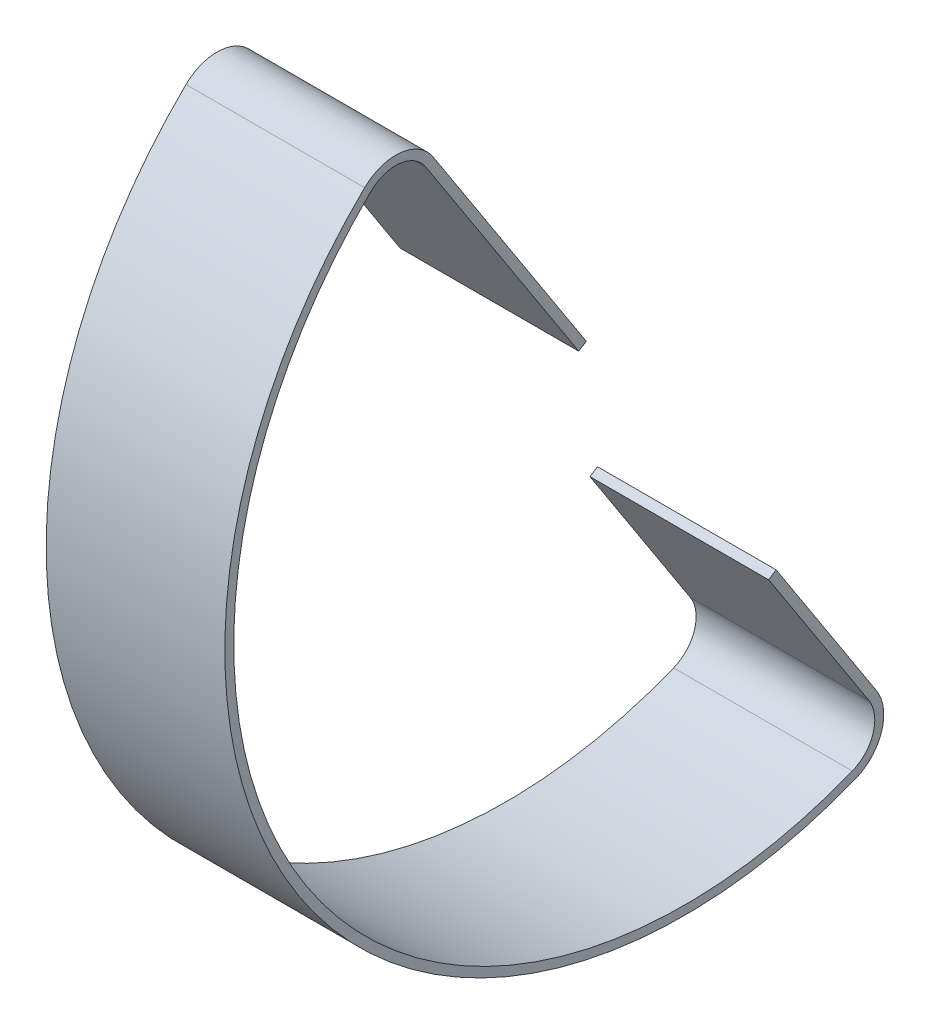
SolidWorks part; units mm, degrees
ref_plane "Front Plane" through (0, 0, 0) normal (0, 0, 1) x (1, 0, 0)
ref_plane "Top Plane" through (0, 0, 0) normal (0, 1, 0) x (1, 0, 0)
ref_plane "Right Plane" through (0, 0, 0) normal (1, 0, 0) x (0, 0, -1)
ref_plane "Plane1" through (1981.2, 0, 0) normal (1, 0, 0) x (0, 0, -1)
sketch "Sketch2" plane through (1981.2, 0, 0) normal (1, 0, 0) x (0, 0, -1)
  line L0 (221.3296, 149.9357) -> (209.5008, 142.2673) construction
  line L1 (221.3296, 149.9357) -> (209.184, 168.6708) construction
  line L2 (221.3296, 149.9357) -> (209.184, 168.6708) construction
  line L3 (273.5917, 69.3195) -> (285.7374, 50.5844) construction
  line L4 (273.5917, 69.3195) -> (285.7374, 50.5844) construction
  line L5 (220.4661, 151.2678) -> (176.9489, 218.3946)
  line L6 (274.4553, 67.9874) -> (303.0021, 23.953)
  line L7 (313.9939, 6.9977) -> (307.8258, 16.5121) construction
  line L8 (273.5917, 69.3195) -> (265.5737, 64.1215) construction
  line L9 (165.7975, 235.5961) -> (172.2848, 225.5893) construction
  line L10 (247.9458, 109.942) -> (151.6337, 47.5045) construction
  line L11 (151.6337, 47.5045) -> (142.0377, 41.2836) construction
  arc A0 (157.4526, 220.6047) -> (297.0616, 5.2526) centre (248.4911, 126.6943) ccw
  arc A1 (297.0616, 5.2526) -> (303.0021, 23.953) centre (292.3455, 17.0445) ccw
  arc A2 (176.9489, 218.3946) -> (157.4526, 220.6047) centre (166.2923, 211.4861) ccw
  spline S11 degree 3 poles (716.4378, 3936.626) (-41.01, 922.5586) (-45.8421, 102.7973) (199.57, -1.0271) (203.7349, -2.5525) (212.2057, -5.1923) (216.5116, -6.3067) (221.9842, -7.4366) (223.0832, -7.6494) (225.2905, -8.0483) (226.4002, -8.2347) (229.7298, -8.7513) (231.9491, -9.0392) (238.6058, -9.7364) (247.4783, -10.2233) (256.3445, -9.8408) (262.9919, -9.2245) (265.2072, -8.964) (268.5297, -8.4895) (269.6371, -8.3173) (271.8517, -7.9447) (272.9592, -7.7441) (278.4654, -6.6762) (282.7945, -5.61) (291.3052, -3.0674) (295.4869, -1.5909) (303.7034, 1.7715) (307.7383, 3.6574) (313.6773, 6.8016) (315.6425, 7.9051) (319.4945, 10.1955) (321.3853, 11.3842) (326.954, 15.0783) (334.1028, 20.3445) (340.7075, 26.2822) (345.4543, 30.9907) (347.0021, 32.6028) (349.271, 35.086) (350.0194, 35.9257) (351.4935, 37.6212) (352.2185, 38.4763) (355.7849, 42.7884) (358.4496, 46.3546) (363.4124, 53.7139) (365.7105, 57.5069) (369.9395, 65.3203) (371.8705, 69.3405) (374.0477, 74.5122) (374.4716, 75.5549) (375.2914, 77.6441) (375.6877, 78.6918) (376.8361, 81.8437) (377.548, 83.9569) (379.5247, 90.3317) (381.7375, 98.9252) (383.1139, 107.7043) (383.8268, 114.3594) (384.0111, 116.5896) (384.206, 119.9531) (384.2572, 121.077) (384.3321, 123.3185) (384.3557, 124.4376) (384.4056, 130.025) (384.2279, 134.4691) (383.4468, 143.3067) (382.8435, 147.7002) (381.2088, 156.4363) (380.1775, 160.7789) (378.6114, 166.1743) (378.2848, 167.25) (377.6073, 169.3868) (377.2561, 170.4491) (376.1655, 173.6179) (375.3891, 175.7062) (372.914, 181.8996) (371.0697, 185.9333) (366.9956, 193.8116) (364.7657, 197.6562) (361.1252, 203.278) (359.8623, 205.1277) (357.2357, 208.7777) (355.8817, 210.5644) (351.7057, 215.8037) (348.7675, 219.1395) (342.5889, 225.5033) (339.3485, 228.5312) (332.5628, 234.2766) (329.0156, 236.9953) (49.0165, 430.2441) (-881.9041, -433.1454) (-2551.1811, -2485.4465) knots -1.810739 -1.810739 -1.810739 -1.810739 0.03125 0.03125 0.0625 0.0625 0.09375 0.09375 0.101562 0.101562 0.109375 0.109375 0.125 0.125 0.15625 0.1875 0.1875 0.203125 0.203125 0.210937 0.210937 0.21875 0.21875 0.25 0.25 0.28125 0.28125 0.3125 0.3125 0.328125 0.328125 0.34375 0.34375 0.375 0.40625 0.40625 0.421875 0.421875 0.429687 0.429687 0.4375 0.4375 0.46875 0.46875 0.5 0.5 0.53125 0.53125 0.539063 0.539063 0.546875 0.546875 0.5625 0.5625 0.59375 0.625 0.625 0.640625 0.640625 0.648438 0.648438 0.65625 0.65625 0.6875 0.6875 0.71875 0.71875 0.75 0.75 0.757813 0.757813 0.765625 0.765625 0.78125 0.78125 0.8125 0.8125 0.84375 0.84375 0.859375 0.859375 0.875 0.875 0.90625 0.90625 0.9375 0.9375 0.96875 0.96875 3.30132 3.30132 3.30132 3.30132 only from (183.4088, 6.5279) to (313.8564, 246.6465)
  spline S12 degree 3 poles (183.4088, 6.5279) (187.3587, 4.3756) (191.3819, 2.437) (199.57, -1.0271) (203.7349, -2.5525) (212.2057, -5.1923) (216.5116, -6.3067) (221.9842, -7.4366) (223.0832, -7.6494) (225.2905, -8.0483) (226.4002, -8.2347) (229.7298, -8.7513) (231.9491, -9.0392) (238.6058, -9.7364) (247.4783, -10.2233) (256.3445, -9.8408) (262.9919, -9.2245) (265.2072, -8.964) (268.5297, -8.4895) (269.6371, -8.3173) (271.8517, -7.9447) (272.9592, -7.7441) (278.4654, -6.6762) (282.7945, -5.61) (291.3052, -3.0674) (295.4869, -1.5909) (303.7034, 1.7715) (307.7383, 3.6574) (313.6773, 6.8016) (315.6425, 7.9051) (319.4945, 10.1955) (321.3853, 11.3842) (326.954, 15.0783) (334.1028, 20.3445) (340.7075, 26.2822) (345.4543, 30.9907) (347.0021, 32.6028) (349.271, 35.086) (350.0194, 35.9257) (351.4935, 37.6212) (352.2185, 38.4763) (355.7849, 42.7884) (358.4496, 46.3546) (363.4124, 53.7139) (365.7105, 57.5069) (369.9395, 65.3203) (371.8705, 69.3405) (374.0477, 74.5122) (374.4716, 75.5549) (375.2914, 77.6441) (375.6877, 78.6918) (376.8361, 81.8437) (377.548, 83.9569) (379.5247, 90.3317) (381.7375, 98.9252) (383.1139, 107.7043) (383.8268, 114.3594) (384.0111, 116.5896) (384.206, 119.9531) (384.2572, 121.077) (384.3321, 123.3185) (384.3557, 124.4376) (384.4056, 130.025) (384.2279, 134.4691) (383.4468, 143.3067) (382.8435, 147.7002) (381.2088, 156.4363) (380.1775, 160.7789) (378.6114, 166.1743) (378.2848, 167.25) (377.6073, 169.3868) (377.2561, 170.4491) (376.1655, 173.6179) (375.3891, 175.7062) (372.914, 181.8996) (371.0697, 185.9333) (366.9956, 193.8116) (364.7657, 197.6562) (361.1252, 203.278) (359.8623, 205.1277) (357.2357, 208.7777) (355.8817, 210.5644) (351.7057, 215.8037) (348.7675, 219.1395) (342.5889, 225.5033) (339.3485, 228.5312) (332.5628, 234.2766) (329.0156, 236.9953) (321.6123, 242.1048) (317.7932, 244.4704) (313.8564, 246.6465) knots 0 0 0 0 0.03125 0.03125 0.0625 0.0625 0.09375 0.09375 0.101562 0.101562 0.109375 0.109375 0.125 0.125 0.15625 0.1875 0.1875 0.203125 0.203125 0.210937 0.210937 0.21875 0.21875 0.25 0.25 0.28125 0.28125 0.3125 0.3125 0.328125 0.328125 0.34375 0.34375 0.375 0.40625 0.40625 0.421875 0.421875 0.429687 0.429687 0.4375 0.4375 0.46875 0.46875 0.5 0.5 0.53125 0.53125 0.539063 0.539063 0.546875 0.546875 0.5625 0.5625 0.59375 0.625 0.625 0.640625 0.640625 0.648438 0.648438 0.65625 0.65625 0.6875 0.6875 0.71875 0.71875 0.75 0.75 0.757813 0.757813 0.765625 0.765625 0.78125 0.78125 0.8125 0.8125 0.84375 0.84375 0.859375 0.859375 0.875 0.875 0.90625 0.90625 0.9375 0.9375 0.96875 0.96875 1 1 1 1 construction
  spline S13 degree 3 poles (-242.5395, -3680.1608) (532.8048, -671.0788) (542.6093, 149.0677) (297.6784, 254.3238) (293.5061, 255.8778) (285.0171, 258.5726) (280.7003, 259.7133) (275.2117, 260.8746) (274.1094, 261.0936) (271.8953, 261.5048) (270.782, 261.6972) (267.443, 262.2314) (265.217, 262.5306) (258.5394, 263.2607) (249.6363, 263.7882) (240.7343, 263.4398) (234.0581, 262.8463) (231.8328, 262.593) (228.4949, 262.1285) (227.3823, 261.9595) (225.1571, 261.5931) (224.0452, 261.3957) (218.5166, 260.3429) (214.169, 259.2871) (205.6195, 256.7613) (201.4177, 255.2913) (193.1597, 251.9376) (189.1035, 250.054) (183.1315, 246.9097) (181.1566, 245.8063) (177.2874, 243.5165) (175.3879, 242.3277) (169.7931, 238.6317) (162.6093, 233.359) (155.9696, 227.4065) (151.1969, 222.6832) (149.6406, 221.0656) (147.359, 218.5732) (146.6064, 217.7303) (145.1266, 216.0311) (144.3986, 215.1739) (140.818, 210.8513) (138.1421, 207.2748) (133.1582, 199.8912) (130.8502, 196.0841) (126.6032, 188.2385) (124.6641, 184.2) (122.4784, 179.0026) (122.0536, 177.9566) (121.2326, 175.8611) (120.8357, 174.8103) (119.6855, 171.6484) (118.9728, 169.5282) (116.994, 163.1312) (115.8872, 158.8181) (114.0946, 150.0958) (113.4088, 145.6866) (112.7023, 138.9994) (112.5206, 136.758) (112.2671, 132.2503) (112.1964, 130.0028) (112.1486, 123.2788) (112.3356, 118.8209) (113.1385, 109.9533) (113.7544, 105.5437) (115.0024, 98.9659) (115.4726, 96.7794) (116.2603, 93.5089) (116.5366, 92.4203) (117.117, 90.2462) (117.4215, 89.1595) (119.0097, 83.7486) (120.4827, 79.5175) (123.8202, 71.2447) (125.6848, 67.2028) (129.8041, 59.3075) (132.0588, 55.454) (135.127, 50.7579) (135.7532, 49.8247) (137.0308, 47.9705) (137.6833, 47.0483) (139.6701, 44.3124) (141.0345, 42.5284) (145.2445, 37.2943) (151.1692, 30.6289) (157.7065, 24.5799) (162.8419, 20.2771) (164.5926, 18.8819) (167.2777, 16.8487) (168.1826, 16.1809) (170.0125, 14.8654) (170.9378, 14.2174) (443.8284, -171.8536) (1345.0037, 655.8308) (3034.7171, 2753.1631) knots -1.804531 -1.804531 -1.804531 -1.804531 0.03125 0.03125 0.0625 0.0625 0.09375 0.09375 0.101562 0.101562 0.109375 0.109375 0.125 0.125 0.15625 0.1875 0.1875 0.203125 0.203125 0.210937 0.210937 0.21875 0.21875 0.25 0.25 0.28125 0.28125 0.3125 0.3125 0.328125 0.328125 0.34375 0.34375 0.375 0.40625 0.40625 0.421875 0.421875 0.429687 0.429687 0.4375 0.4375 0.46875 0.46875 0.5 0.5 0.53125 0.53125 0.539062 0.539062 0.546875 0.546875 0.5625 0.5625 0.59375 0.59375 0.625 0.625 0.640625 0.640625 0.65625 0.65625 0.6875 0.6875 0.71875 0.71875 0.734375 0.734375 0.742187 0.742187 0.75 0.75 0.78125 0.78125 0.8125 0.8125 0.84375 0.84375 0.851562 0.851562 0.859375 0.859375 0.875 0.875 0.90625 0.9375 0.9375 0.953125 0.953125 0.960937 0.960937 0.96875 0.96875 3.24847 3.24847 3.24847 3.24847 only from (313.8564, 246.6465) to (183.4088, 6.5279)
  spline S14 degree 3 poles (313.8564, 246.6465) (309.9046, 248.8308) (305.8776, 250.8003) (297.6784, 254.3238) (293.5061, 255.8778) (285.0171, 258.5726) (280.7003, 259.7133) (275.2117, 260.8746) (274.1094, 261.0936) (271.8953, 261.5048) (270.782, 261.6972) (267.443, 262.2314) (265.217, 262.5306) (258.5394, 263.2607) (249.6363, 263.7882) (240.7343, 263.4398) (234.0581, 262.8463) (231.8328, 262.593) (228.4949, 262.1285) (227.3823, 261.9595) (225.1571, 261.5931) (224.0452, 261.3957) (218.5166, 260.3429) (214.169, 259.2871) (205.6195, 256.7613) (201.4177, 255.2913) (193.1597, 251.9376) (189.1035, 250.054) (183.1315, 246.9097) (181.1566, 245.8063) (177.2874, 243.5165) (175.3879, 242.3277) (169.7931, 238.6317) (162.6093, 233.359) (155.9696, 227.4065) (151.1969, 222.6832) (149.6406, 221.0656) (147.359, 218.5732) (146.6064, 217.7303) (145.1266, 216.0311) (144.3986, 215.1739) (140.818, 210.8513) (138.1421, 207.2748) (133.1582, 199.8912) (130.8502, 196.0841) (126.6032, 188.2385) (124.6641, 184.2) (122.4784, 179.0026) (122.0536, 177.9566) (121.2326, 175.8611) (120.8357, 174.8103) (119.6855, 171.6484) (118.9728, 169.5282) (116.994, 163.1312) (115.8872, 158.8181) (114.0946, 150.0958) (113.4088, 145.6866) (112.7023, 138.9994) (112.5206, 136.758) (112.2671, 132.2503) (112.1964, 130.0028) (112.1486, 123.2788) (112.3356, 118.8209) (113.1385, 109.9533) (113.7544, 105.5437) (115.0024, 98.9659) (115.4726, 96.7794) (116.2603, 93.5089) (116.5366, 92.4203) (117.117, 90.2462) (117.4215, 89.1595) (119.0097, 83.7486) (120.4827, 79.5175) (123.8202, 71.2447) (125.6848, 67.2028) (129.8041, 59.3075) (132.0588, 55.454) (135.127, 50.7579) (135.7532, 49.8247) (137.0308, 47.9705) (137.6833, 47.0483) (139.6701, 44.3124) (141.0345, 42.5284) (145.2445, 37.2943) (151.1692, 30.6289) (157.7065, 24.5799) (162.8419, 20.2771) (164.5926, 18.8819) (167.2777, 16.8487) (168.1826, 16.1809) (170.0125, 14.8654) (170.9378, 14.2174) (175.5978, 11.04) (179.444, 8.6885) (183.4088, 6.5279) knots 0 0 0 0 0.03125 0.03125 0.0625 0.0625 0.09375 0.09375 0.101562 0.101562 0.109375 0.109375 0.125 0.125 0.15625 0.1875 0.1875 0.203125 0.203125 0.210937 0.210937 0.21875 0.21875 0.25 0.25 0.28125 0.28125 0.3125 0.3125 0.328125 0.328125 0.34375 0.34375 0.375 0.40625 0.40625 0.421875 0.421875 0.429687 0.429687 0.4375 0.4375 0.46875 0.46875 0.5 0.5 0.53125 0.53125 0.539062 0.539062 0.546875 0.546875 0.5625 0.5625 0.59375 0.59375 0.625 0.625 0.640625 0.640625 0.65625 0.65625 0.6875 0.6875 0.71875 0.71875 0.734375 0.734375 0.742187 0.742187 0.75 0.75 0.78125 0.78125 0.8125 0.8125 0.84375 0.84375 0.851562 0.851562 0.859375 0.859375 0.875 0.875 0.90625 0.9375 0.9375 0.953125 0.953125 0.960937 0.960937 0.96875 0.96875 1 1 1 1 construction
  spline S15 degree 3 poles (-283.106, -3688.3408) (508.334, -662.837) (526.1426, 143.4053) (293.3653, 243.1749) (289.5491, 244.5923) (281.7849, 247.0493) (277.837, 248.0889) (272.8177, 249.1464) (271.8096, 249.3458) (269.7849, 249.7201) (268.7669, 249.8952) (265.7133, 250.3813) (263.6778, 250.6532) (257.5713, 251.316) (249.4303, 251.7922) (241.291, 251.468) (235.1872, 250.9213) (233.1527, 250.6884) (230.1011, 250.2617) (229.0839, 250.1066) (227.0497, 249.7703) (226.033, 249.5891) (220.9782, 248.6234) (217.0033, 247.6557) (209.1872, 245.3418) (205.3459, 243.9957) (197.7969, 240.9256) (194.0891, 239.2017) (188.6302, 236.3247) (186.8249, 235.315) (183.2875, 233.2197) (181.551, 232.132) (176.4364, 228.7505) (169.8693, 223.927) (163.7999, 218.4829) (159.4374, 214.1635) (158.0148, 212.6842) (155.9293, 210.4051) (155.2414, 209.6343) (153.8884, 208.0802) (153.2229, 207.2963) (149.9492, 203.3428) (147.5028, 200.0721) (142.9464, 193.3202) (140.8363, 189.8391) (136.9535, 182.6657) (135.1806, 178.9735) (133.1822, 174.2221) (132.7937, 173.2655) (132.0427, 171.3492) (131.6797, 170.3883) (130.6277, 167.4969) (129.9758, 165.5582) (128.1657, 159.7088) (127.1531, 155.7651) (125.5126, 147.7903) (124.8848, 143.7592) (124.2373, 137.6458) (124.0706, 135.5968) (123.8376, 131.4761) (123.7722, 129.4199) (123.7265, 123.2709) (123.896, 119.1943) (124.6269, 111.0857) (125.1883, 107.0537) (126.3265, 101.0393) (126.7553, 99.0401) (127.7134, 95.0532) (128.2432, 93.0636) (129.9829, 87.1241) (131.3277, 83.254) (134.375, 75.687) (136.0776, 71.9901) (139.8389, 64.7687) (141.8976, 61.2443) (144.6991, 56.9491) (145.2709, 56.0957) (146.4374, 54.3999) (147.0331, 53.5564) (148.8483, 51.0526) (150.0947, 49.42) (153.9409, 44.63) (159.3536, 38.5301) (165.3255, 32.9941) (170.0165, 29.0559) (171.6156, 27.7789) (174.0683, 25.9178) (174.8948, 25.3065) (176.5662, 24.1024) (177.4116, 23.509) (439.002, -155.2606) (1332.8814, 685.8356) (3014.0431, 2794.3665) knots -1.877287 -1.877287 -1.877287 -1.877287 0.03125 0.03125 0.0625 0.0625 0.09375 0.09375 0.101563 0.101563 0.109375 0.109375 0.125 0.125 0.15625 0.1875 0.1875 0.203125 0.203125 0.210938 0.210938 0.21875 0.21875 0.25 0.25 0.28125 0.28125 0.3125 0.3125 0.328125 0.328125 0.34375 0.34375 0.375 0.40625 0.40625 0.421875 0.421875 0.429688 0.429688 0.4375 0.4375 0.46875 0.46875 0.5 0.5 0.53125 0.53125 0.539063 0.539063 0.546875 0.546875 0.5625 0.5625 0.59375 0.59375 0.625 0.625 0.640625 0.640625 0.65625 0.65625 0.6875 0.6875 0.71875 0.71875 0.734375 0.734375 0.75 0.75 0.78125 0.78125 0.8125 0.8125 0.84375 0.84375 0.851563 0.851563 0.859375 0.859375 0.875 0.875 0.90625 0.9375 0.9375 0.953125 0.953125 0.960938 0.960938 0.96875 0.96875 3.360625 3.360625 3.360625 3.360625 only from (308.1647, 236.1696) to (188.8075, 16.4655)
  spline S16 degree 3 poles (308.1647, 236.1696) (304.5493, 238.1632) (300.8654, 239.9603) (293.3653, 243.1749) (289.5491, 244.5923) (281.7849, 247.0493) (277.837, 248.0889) (272.8177, 249.1464) (271.8096, 249.3458) (269.7849, 249.7201) (268.7669, 249.8952) (265.7133, 250.3813) (263.6778, 250.6532) (257.5713, 251.316) (249.4303, 251.7922) (241.291, 251.468) (235.1872, 250.9213) (233.1527, 250.6884) (230.1011, 250.2617) (229.0839, 250.1066) (227.0497, 249.7703) (226.033, 249.5891) (220.9782, 248.6234) (217.0033, 247.6557) (209.1872, 245.3418) (205.3459, 243.9957) (197.7969, 240.9256) (194.0891, 239.2017) (188.6302, 236.3247) (186.8249, 235.315) (183.2875, 233.2197) (181.551, 232.132) (176.4364, 228.7505) (169.8693, 223.927) (163.7999, 218.4829) (159.4374, 214.1635) (158.0148, 212.6842) (155.9293, 210.4051) (155.2414, 209.6343) (153.8884, 208.0802) (153.2229, 207.2963) (149.9492, 203.3428) (147.5028, 200.0721) (142.9464, 193.3202) (140.8363, 189.8391) (136.9535, 182.6657) (135.1806, 178.9735) (133.1822, 174.2221) (132.7937, 173.2655) (132.0427, 171.3492) (131.6797, 170.3883) (130.6277, 167.4969) (129.9758, 165.5582) (128.1657, 159.7088) (127.1531, 155.7651) (125.5126, 147.7903) (124.8848, 143.7592) (124.2373, 137.6458) (124.0706, 135.5968) (123.8376, 131.4761) (123.7722, 129.4199) (123.7265, 123.2709) (123.896, 119.1943) (124.6269, 111.0857) (125.1883, 107.0537) (126.3265, 101.0393) (126.7553, 99.0401) (127.7134, 95.0532) (128.2432, 93.0636) (129.9829, 87.1241) (131.3277, 83.254) (134.375, 75.687) (136.0776, 71.9901) (139.8389, 64.7687) (141.8976, 61.2443) (144.6991, 56.9491) (145.2709, 56.0957) (146.4374, 54.3999) (147.0331, 53.5564) (148.8483, 51.0526) (150.0947, 49.42) (153.9409, 44.63) (159.3536, 38.5301) (165.3255, 32.9941) (170.0165, 29.0559) (171.6156, 27.7789) (174.0683, 25.9178) (174.8948, 25.3065) (176.5662, 24.1024) (177.4116, 23.509) (181.6698, 20.599) (185.1844, 18.445) (188.8075, 16.4655) knots 0 0 0 0 0.03125 0.03125 0.0625 0.0625 0.09375 0.09375 0.101563 0.101563 0.109375 0.109375 0.125 0.125 0.15625 0.1875 0.1875 0.203125 0.203125 0.210938 0.210938 0.21875 0.21875 0.25 0.25 0.28125 0.28125 0.3125 0.3125 0.328125 0.328125 0.34375 0.34375 0.375 0.40625 0.40625 0.421875 0.421875 0.429688 0.429688 0.4375 0.4375 0.46875 0.46875 0.5 0.5 0.53125 0.53125 0.539063 0.539063 0.546875 0.546875 0.5625 0.5625 0.59375 0.59375 0.625 0.625 0.640625 0.640625 0.65625 0.65625 0.6875 0.6875 0.71875 0.71875 0.734375 0.734375 0.75 0.75 0.78125 0.78125 0.8125 0.8125 0.84375 0.84375 0.851563 0.851563 0.859375 0.859375 0.875 0.875 0.90625 0.9375 0.9375 0.953125 0.953125 0.960938 0.960938 0.96875 0.96875 1 1 1 1 construction
  spline S17 degree 3 poles (-2751.1525, 2792.7474) (1122.9295, -127.9602) (498.065, 247.5508) (102.2279, 91.7606) (97.9404, 89.9983) (91.5629, 87.2263) (89.446, 86.281) (86.29, 84.8167) (85.2412, 84.3208) (13.5509, 49.5235) (-37.8649, -30.7706) (1405.2472, -3686.3529) knots -22.187167 -22.187167 -22.187167 -22.187167 0.5 0.5 0.75 0.75 0.875 0.875 0.9375 0.9375 5.166072 5.166072 5.166072 5.166072 only from (132.7178, 102.9159) to (81.0819, 82.252)
  spline S18 degree 3 poles (132.7178, 102.9159) (123.9131, 99.9934) (115.171, 96.8546) (102.2279, 91.7606) (97.9404, 89.9983) (91.5629, 87.2263) (89.446, 86.281) (86.29, 84.8167) (85.2412, 84.3208) (83.1528, 83.3072) (82.1129, 82.7903) (81.0819, 82.252) knots 0 0 0 0 0.5 0.5 0.75 0.75 0.875 0.875 0.9375 0.9375 1 1 1 1 construction
  spline S19 degree 3 poles (764.9531, 3943.1565) (-14.832, 914.4258) (-29.4722, 108.4213) (203.5969, 9.5325) (207.4088, 8.132) (215.1622, 5.7075) (219.1037, 4.6835) (224.1135, 3.6445) (225.1196, 3.4487) (227.1403, 3.0817) (228.1562, 2.9102) (231.2042, 2.4345) (233.2358, 2.1693) (239.3299, 1.5259) (247.4528, 1.0737) (255.571, 1.4181) (261.6577, 1.9783) (263.6863, 2.2155) (266.7288, 2.6481) (267.7429, 2.8051) (269.7709, 3.1451) (270.785, 3.3281) (275.8265, 4.3028) (279.7904, 5.2766) (287.5837, 7.6004) (291.413, 8.9503) (298.9375, 12.0256) (302.6327, 13.7509) (308.0721, 16.6279) (309.8717, 17.6376) (313.3989, 19.7332) (315.1302, 20.8209) (320.2294, 24.2012) (326.7758, 29.0209) (332.8245, 34.4563) (337.1717, 38.7669) (338.5892, 40.2429) (340.6672, 42.5166) (341.3527, 43.2855) (342.7023, 44.8374) (343.3661, 45.6202) (346.6313, 49.5673) (349.0711, 52.832) (353.6151, 59.5695) (355.7193, 63.0423) (359.5915, 70.1966) (361.3595, 73.878) (363.3529, 78.6142) (363.7409, 79.5689) (364.4911, 81.4814) (364.8538, 82.4405) (365.9048, 85.326) (366.5562, 87.2606) (368.3651, 93.0968) (370.3898, 100.9649) (371.6483, 109.0038) (372.2996, 115.0983) (372.4678, 117.1407) (372.6454, 120.2209) (372.692, 121.2497) (372.7599, 123.3015) (372.7812, 124.3259) (372.8253, 129.4407) (372.6612, 133.5091) (371.9432, 141.5999) (371.3893, 145.6224) (369.8891, 153.6213) (368.9428, 157.5976) (367.2188, 163.5263) (366.5969, 165.4835) (365.2638, 169.3503) (364.552, 171.2616) (362.2831, 176.9303) (360.5926, 180.6223) (356.858, 187.8336) (354.8139, 191.3527) (351.4766, 196.4989) (350.3187, 198.1924) (347.911, 201.5331) (346.671, 203.1668) (342.8449, 207.9599) (337.4608, 214.0634) (331.5223, 219.6036) (326.8586, 223.5454) (325.269, 224.8237) (322.0186, 227.3081) (320.3563, 228.5151) (55.1067, 411.2126) (-858.655, -454.0579) (-2525.9478, -2532.4739) knots -1.881423 -1.881423 -1.881423 -1.881423 0.03125 0.03125 0.0625 0.0625 0.09375 0.09375 0.101562 0.101562 0.109375 0.109375 0.125 0.125 0.15625 0.1875 0.1875 0.203125 0.203125 0.210938 0.210938 0.21875 0.21875 0.25 0.25 0.28125 0.28125 0.3125 0.3125 0.328125 0.328125 0.34375 0.34375 0.375 0.40625 0.40625 0.421875 0.421875 0.429687 0.429687 0.4375 0.4375 0.46875 0.46875 0.5 0.5 0.53125 0.53125 0.539062 0.539062 0.546875 0.546875 0.5625 0.5625 0.59375 0.625 0.625 0.640625 0.640625 0.648437 0.648437 0.65625 0.65625 0.6875 0.6875 0.71875 0.71875 0.75 0.75 0.765625 0.765625 0.78125 0.78125 0.8125 0.8125 0.84375 0.84375 0.859375 0.859375 0.875 0.875 0.90625 0.9375 0.9375 0.953125 0.953125 0.96875 0.96875 3.397555 3.397555 3.397555 3.397555 only from (188.8075, 16.4655) to (308.1647, 236.1696)
  spline S20 degree 3 poles (188.8075, 16.4655) (192.4217, 14.4908) (196.1034, 12.7119) (203.5969, 9.5325) (207.4088, 8.132) (215.1622, 5.7075) (219.1037, 4.6835) (224.1135, 3.6445) (225.1196, 3.4487) (227.1403, 3.0817) (228.1562, 2.9102) (231.2042, 2.4345) (233.2358, 2.1693) (239.3299, 1.5259) (247.4528, 1.0737) (255.571, 1.4181) (261.6577, 1.9783) (263.6863, 2.2155) (266.7288, 2.6481) (267.7429, 2.8051) (269.7709, 3.1451) (270.785, 3.3281) (275.8265, 4.3028) (279.7904, 5.2766) (287.5837, 7.6004) (291.413, 8.9503) (298.9375, 12.0256) (302.6327, 13.7509) (308.0721, 16.6279) (309.8717, 17.6376) (313.3989, 19.7332) (315.1302, 20.8209) (320.2294, 24.2012) (326.7758, 29.0209) (332.8245, 34.4563) (337.1717, 38.7669) (338.5892, 40.2429) (340.6672, 42.5166) (341.3527, 43.2855) (342.7023, 44.8374) (343.3661, 45.6202) (346.6313, 49.5673) (349.0711, 52.832) (353.6151, 59.5695) (355.7193, 63.0423) (359.5915, 70.1966) (361.3595, 73.878) (363.3529, 78.6142) (363.7409, 79.5689) (364.4911, 81.4814) (364.8538, 82.4405) (365.9048, 85.326) (366.5562, 87.2606) (368.3651, 93.0968) (370.3898, 100.9649) (371.6483, 109.0038) (372.2996, 115.0983) (372.4678, 117.1407) (372.6454, 120.2209) (372.692, 121.2497) (372.7599, 123.3015) (372.7812, 124.3259) (372.8253, 129.4407) (372.6612, 133.5091) (371.9432, 141.5999) (371.3893, 145.6224) (369.8891, 153.6213) (368.9428, 157.5976) (367.2188, 163.5263) (366.5969, 165.4835) (365.2638, 169.3503) (364.552, 171.2616) (362.2831, 176.9303) (360.5926, 180.6223) (356.858, 187.8336) (354.8139, 191.3527) (351.4766, 196.4989) (350.3187, 198.1924) (347.911, 201.5331) (346.671, 203.1668) (342.8449, 207.9599) (337.4608, 214.0634) (331.5223, 219.6036) (326.8586, 223.5454) (325.269, 224.8237) (322.0186, 227.3081) (320.3563, 228.5151) (315.2698, 232.0185) (311.7712, 234.1809) (308.1647, 236.1696) knots 0 0 0 0 0.03125 0.03125 0.0625 0.0625 0.09375 0.09375 0.101562 0.101562 0.109375 0.109375 0.125 0.125 0.15625 0.1875 0.1875 0.203125 0.203125 0.210938 0.210938 0.21875 0.21875 0.25 0.25 0.28125 0.28125 0.3125 0.3125 0.328125 0.328125 0.34375 0.34375 0.375 0.40625 0.40625 0.421875 0.421875 0.429687 0.429687 0.4375 0.4375 0.46875 0.46875 0.5 0.5 0.53125 0.53125 0.539062 0.539062 0.546875 0.546875 0.5625 0.5625 0.59375 0.625 0.625 0.640625 0.640625 0.648437 0.648437 0.65625 0.65625 0.6875 0.6875 0.71875 0.71875 0.75 0.75 0.765625 0.765625 0.78125 0.78125 0.8125 0.8125 0.84375 0.84375 0.859375 0.859375 0.875 0.875 0.90625 0.9375 0.9375 0.953125 0.953125 0.96875 0.96875 1 1 1 1 construction
  spline S21 degree 3 poles (2769.9179, -2964.6264) (54.3339, -168.8273) (38.2566, -57.489) (83.8558, -5.9808) (84.5785, -5.1969) (86.7794, -2.8779) (88.2901, -1.3751) (91.3667, 1.5757) (92.9329, 3.0232) (96.1079, 5.8762) (97.7165, 7.2812) (102.5853, 11.4344) (105.8915, 14.125) (112.6011, 19.3806) (116.0049, 21.9449) (122.8996, 26.9607) (126.3922, 29.4128) (133.4527, 34.2065) (137.0182, 36.5462) (646.9668, 360.422) (1813.8639, -388.0279) (148.3469, 3451.8328) knots -1.951853 -1.951853 -1.951853 -1.951853 0.03125 0.03125 0.0625 0.0625 0.125 0.125 0.1875 0.1875 0.25 0.25 0.375 0.375 0.5 0.5 0.625 0.625 0.75 0.75 18.337148 18.337148 18.337148 18.337148 only from (81.0819, -9.2325) to (162.6006, 51.9137)
  spline S22 degree 3 poles (81.0819, -9.2325) (81.7487, -8.3931) (82.4409, -7.5789) (83.8558, -5.9808) (84.5785, -5.1969) (86.7794, -2.8779) (88.2901, -1.3751) (91.3667, 1.5757) (92.9329, 3.0232) (96.1079, 5.8762) (97.7165, 7.2812) (102.5853, 11.4344) (105.8915, 14.125) (112.6011, 19.3806) (116.0049, 21.9449) (122.8996, 26.9607) (126.3922, 29.4128) (133.4527, 34.2065) (137.0182, 36.5462) (147.8148, 43.4033) (155.1459, 47.7585) (162.6006, 51.9137) knots 0 0 0 0 0.03125 0.03125 0.0625 0.0625 0.125 0.125 0.1875 0.1875 0.25 0.25 0.375 0.375 0.5 0.5 0.625 0.625 0.75 0.75 1 1 1 1 construction
  spline S23 degree 3 poles (207.2453, 83.5564) (260.0163, 2.1551) (341.4175, 54.9261) (288.6465, 136.3274) (235.8755, 217.7287) (154.4742, 164.9577) (207.2453, 83.5564) (260.0163, 2.1551) (341.4175, 54.9261) knots -0.5 0 0 0 0.5 0.5 0.5 1 1 1 1.5 1.5 1.5 weights 1 0.333333 0.333333 1 0.333333 0.333333 1 0.333333 0.333333 only from (207.2453, 83.5564) to (207.2453, 83.5564) construction
  spline S24 degree 3 poles (207.2453, 83.5564) (260.0163, 2.1551) (341.4175, 54.9261) (288.6465, 136.3274) (235.8755, 217.7287) (154.4742, 164.9577) (207.2453, 83.5564) (260.0163, 2.1551) (341.4175, 54.9261) knots -0.5 0 0 0 0.5 0.5 0.5 1 1 1 1.5 1.5 1.5 weights 1 0.333333 0.333333 1 0.333333 0.333333 1 0.333333 0.333333 only from (207.2453, 83.5564) to (207.2453, 83.5564) construction
  point P19 (169.0411, 230.5927)
  point P22 (310.9099, 11.7549)
  point P29 (146.8357, 44.394)
  point P33 (310.9099, 11.7549)
  point P36 (169.0411, 230.5927)
  dimension "D4" = 12.7
  dimension "D1" = 0
  dimension "D2" = 1.5875
  dimension "D3" = 1.5875
extrude "Extrude-Thin1" add sketch "Sketch2" along normal mid plane 50.8 thin contours L5 A2 A0 A1 L6
equation "\"D3@Sketch2\"=\"D2@Sketch2\""
